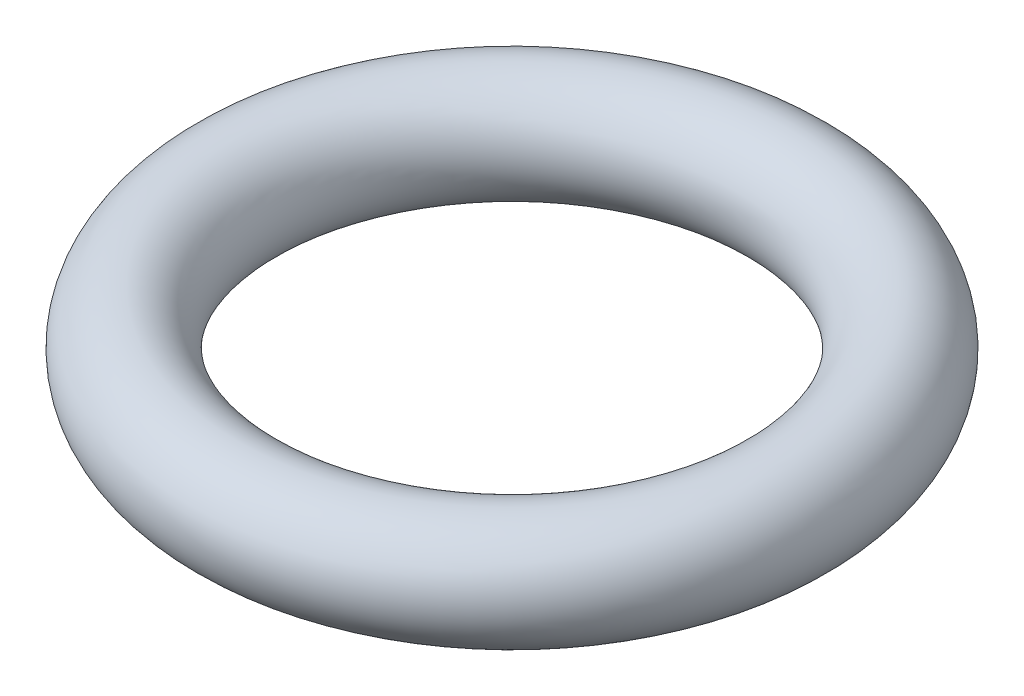
SolidWorks part; units mm, degrees
ref_plane "Front Plane" through (0, 0, 0) normal (0, 0, 1) x (1, 0, 0)
ref_plane "Top Plane" through (0, 0, 0) normal (0, 1, 0) x (1, 0, 0)
ref_plane "Right Plane" through (0, 0, 0) normal (1, 0, 0) x (0, 0, -1)
sketch "Sketch1" plane through (0, 0, 0) normal (0, 0, 1) x (1, 0, 0)
  line L0 (0, 0) -> (4, 0) construction
  line L1 (0, 0) -> (0, 2.6047) construction
  circle A0 centre (4, 0) radius 0.8
  dimension "D1" = 1.6
  dimension "D2" = 4
revolve "Revolve1" add sketch "Sketch1" angle 360 about L1
